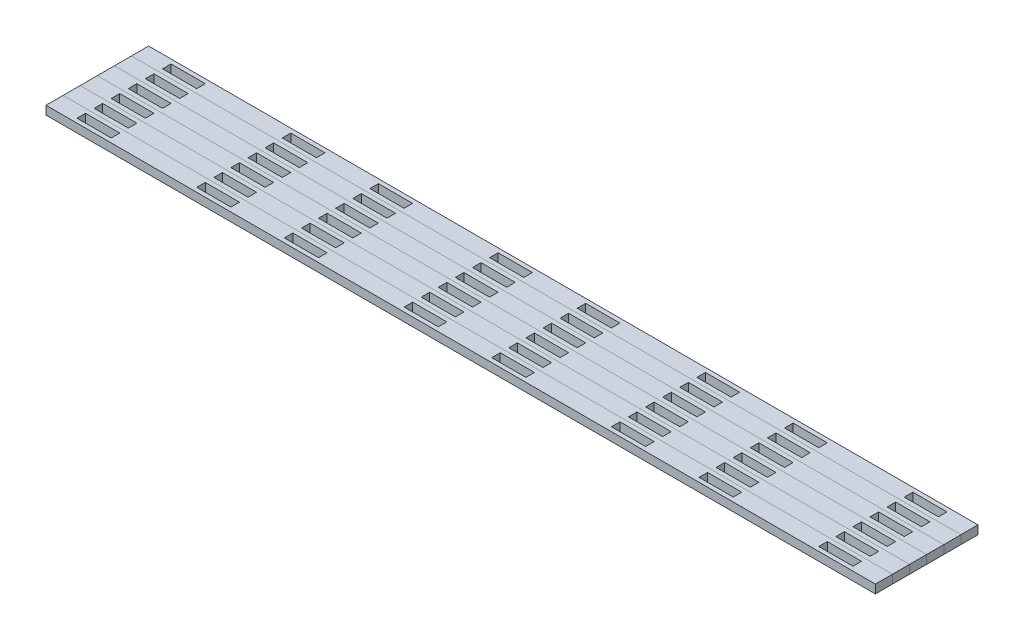
SolidWorks part; units mm, degrees
material "Cedar"
ref_plane "Front Plane" through (0, 0, 0) normal (0, 0, 1) x (1, 0, 0)
ref_plane "Top Plane" through (0, 0, 0) normal (0, 1, 0) x (1, 0, 0)
ref_plane "Right Plane" through (0, 0, 0) normal (1, 0, 0) x (0, 0, -1)
sketch "Sketch1" plane through (0, 0, 0) normal (0, 1, 0) x (1, 0, 0)
  line L1 (-307.9586, 6.35) -> (307.9586, 6.35)
  line L2 (-307.9586, 6.35) -> (-307.9586, -6.35)
  line L3 (-307.9586, -6.35) -> (307.9586, -6.35)
  line L4 (307.9586, 6.35) -> (307.9586, -6.35)
  line L5 (-307.9586, 6.35) -> (307.9586, -6.35) construction
  line L6 (-307.9586, -6.35) -> (307.9586, 6.35) construction
  point P0 (0, 0)
  dimension "D1" = 615.9173
  dimension "D2" = 12.7
extrude "Boss-Extrude1" add sketch "Sketch1" along normal blind 6.35
sketch "Sketch2" plane through (0, 6.35, 0) normal (0, 1, 0) x (1, 0, 0)
  line L0 (-32.5397, 0) -> (32.5397, 0) construction
  line L1 (-45.2397, 3.175) -> (-19.8397, 3.175)
  line L2 (-45.2397, 3.175) -> (-45.2397, -3.175)
  line L3 (-45.2397, -3.175) -> (-19.8397, -3.175)
  line L4 (-19.8397, 3.175) -> (-19.8397, -3.175)
  line L5 (-45.2397, 3.175) -> (-19.8397, -3.175) construction
  line L6 (-45.2397, -3.175) -> (-19.8397, 3.175) construction
  line L7 (19.8397, 3.175) -> (45.2397, 3.175)
  line L8 (19.8397, 3.175) -> (19.8397, -3.175)
  line L9 (19.8397, -3.175) -> (45.2397, -3.175)
  line L10 (45.2397, 3.175) -> (45.2397, -3.175)
  line L11 (19.8397, 3.175) -> (45.2397, -3.175) construction
  line L12 (19.8397, -3.175) -> (45.2397, 3.175) construction
  line L13 (-108.7397, 0) -> (-45.2397, 0) construction
  line L14 (-134.1397, 3.175) -> (-108.7397, 3.175)
  line L15 (-134.1397, 3.175) -> (-134.1397, -3.175)
  line L16 (-134.1397, -3.175) -> (-108.7397, -3.175)
  line L17 (-108.7397, 3.175) -> (-108.7397, -3.175)
  line L18 (-134.1397, 3.175) -> (-108.7397, -3.175) construction
  line L19 (-134.1397, -3.175) -> (-108.7397, 3.175) construction
  line L20 (108.7397, 3.175) -> (134.1397, 3.175)
  line L21 (108.7397, 3.175) -> (108.7397, -3.175)
  line L22 (108.7397, -3.175) -> (134.1397, -3.175)
  line L23 (134.1397, 3.175) -> (134.1397, -3.175)
  line L24 (108.7397, 3.175) -> (134.1397, -3.175) construction
  line L25 (108.7397, -3.175) -> (134.1397, 3.175) construction
  line L26 (45.2397, 0) -> (108.7397, 0) construction
  point P0 (-32.5397, 0)
  point P5 (32.5397, 0)
  point P12 (0, 0)
  point P13 (121.4397, 0)
  point P16 (-121.4397, 0)
  dimension "D1" = 65.0793
  dimension "D2" = 25.4
  dimension "D3" = 25.4
  dimension "D4" = 6.35
  dimension "D5" = 6.35
  dimension "D6" = 6.35
  dimension "D7" = 25.4
  dimension "D8" = 63.5
  dimension "D9" = 25.4
  dimension "D10" = 6.35
  dimension "D11" = 63.5
extrude "Cut-Extrude1" cut sketch "Sketch2" against normal through all
pattern_linear "LPattern1" count 2 spacing 307.9586 along (1, 0, 0) count 2 spacing 307.9586 along (-1, 0, 0) of "Cut-Extrude1"
pattern_linear "LPattern2" count 6 spacing 12.7 along (0, 0, 1) of bodies 103
